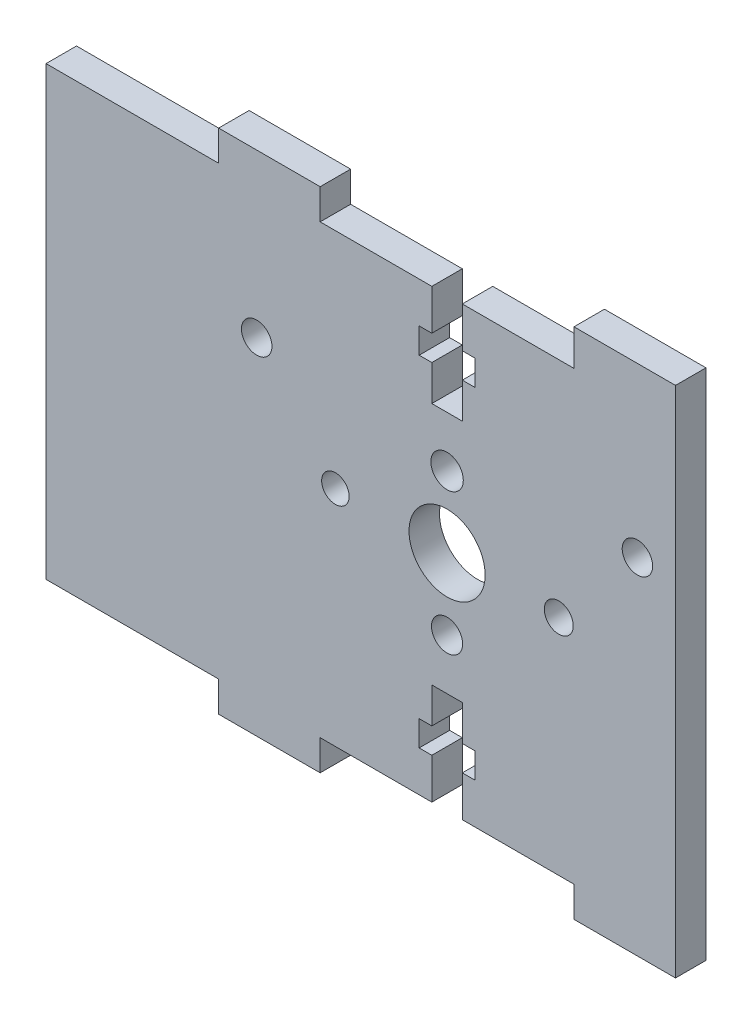
SolidWorks part; units mm, degrees
ref_plane "Front Plane" through (0, 0, 0) normal (0, 0, 1) x (1, 0, 0)
ref_plane "Top Plane" through (0, 0, 0) normal (0, 1, 0) x (1, 0, 0)
ref_plane "Right Plane" through (0, 0, 0) normal (1, 0, 0) x (0, 0, -1)
sketch "Model" plane through (0, 0, 0) normal (0, 0, 1) x (1, 0, 0)
  line L0 (58.24, 47.9) -> (61.24, 47.9)
  line L1 (61.24, 51.4001) -> (62.49, 51.4001)
  line L2 (61.24, 53.9001) -> (62.49, 53.9001)
  line L3 (56.99, 51.4001) -> (58.24, 51.4001)
  line L4 (58.24, 53.9001) -> (56.99, 53.9001)
  line L5 (58.24, 57.9) -> (47.24, 57.9)
  line L6 (61.24, 57.9) -> (72.24, 57.9)
  line L7 (47.24, 57.9) -> (47.24, 60.9)
  line L8 (72.24, 57.9) -> (72.24, 61.4497)
  line L9 (58.24, 57.9) -> (58.24, 53.9001)
  line L10 (56.99, 53.9001) -> (56.99, 51.4001)
  line L11 (58.24, 51.4001) -> (58.24, 47.9)
  line L12 (61.24, 47.9) -> (61.24, 51.4001)
  line L13 (62.49, 51.4001) -> (62.49, 53.9001)
  line L14 (61.24, 53.9001) -> (61.24, 57.9)
  line L16 (58.24, 23.9) -> (61.24, 23.9)
  line L17 (58.24, 20.4) -> (56.99, 20.4)
  line L18 (61.24, 20.4) -> (62.49, 20.4)
  line L19 (62.49, 17.9) -> (61.24, 17.9)
  line L20 (58.24, 17.9) -> (56.99, 17.9)
  line L21 (58.24, 13.9) -> (47.24, 13.9)
  line L22 (61.24, 13.9) -> (72.24, 13.9)
  line L23 (72.24, 61.4497) -> (82.24, 61.4497)
  line L24 (47.24, 10.9) -> (37.24, 10.9)
  line L25 (58.24, 23.9) -> (58.24, 20.4)
  line L26 (56.99, 20.4) -> (56.99, 17.9)
  line L27 (58.24, 17.9) -> (58.24, 13.9)
  line L28 (61.24, 17.9) -> (61.24, 13.9)
  line L29 (62.49, 17.9) -> (62.49, 20.4)
  line L30 (61.24, 20.4) -> (61.24, 23.9)
  line L31 (72.24, 13.9) -> (72.24, 10.9)
  line L32 (47.24, 13.9) -> (47.24, 10.9)
  line L34 (37.24, 60.9) -> (47.24, 60.9)
  line L35 (82.24, 61.4497) -> (82.24, 57.9)
  line L37 (72.24, 10.9) -> (82.24, 10.9)
  line L38 (82.24, 10.9) -> (82.24, 13.9)
  line L43 (37.24, 13.9) -> (37.24, 10.9)
  line L44 (37.24, 57.9) -> (37.24, 60.9)
  line L46 (37.24, 13.9) -> (20.24, 13.9)
  line L47 (20.24, 13.9) -> (20.24, 57.9)
  line L48 (20.24, 57.9) -> (37.24, 57.9)
  line L49 (82.24, 57.9) -> (82.24, 13.9)
  circle A0 centre (59.74, 35.9) radius 3.75
  circle A1 centre (40.99, 44.9) radius 1.5
  circle A2 centre (48.7399, 35.9) radius 1.3532
  circle A3 centre (59.7399, 42.9001) radius 1.5983
  circle A4 centre (59.7399, 28.9) radius 1.5333
  circle A5 centre (70.7399, 35.9001) radius 1.4264
  circle A6 centre (78.49, 44.9) radius 1.5
  dimension "D2" = 6.25
  dimension "D3" = 7.75
  dimension "D1" = 10
  dimension "D4" = 10
  dimension "D5" = 10
  dimension "D6" = 10
extrude "Boss-Extrude1" add sketch "Model" along normal blind 3
